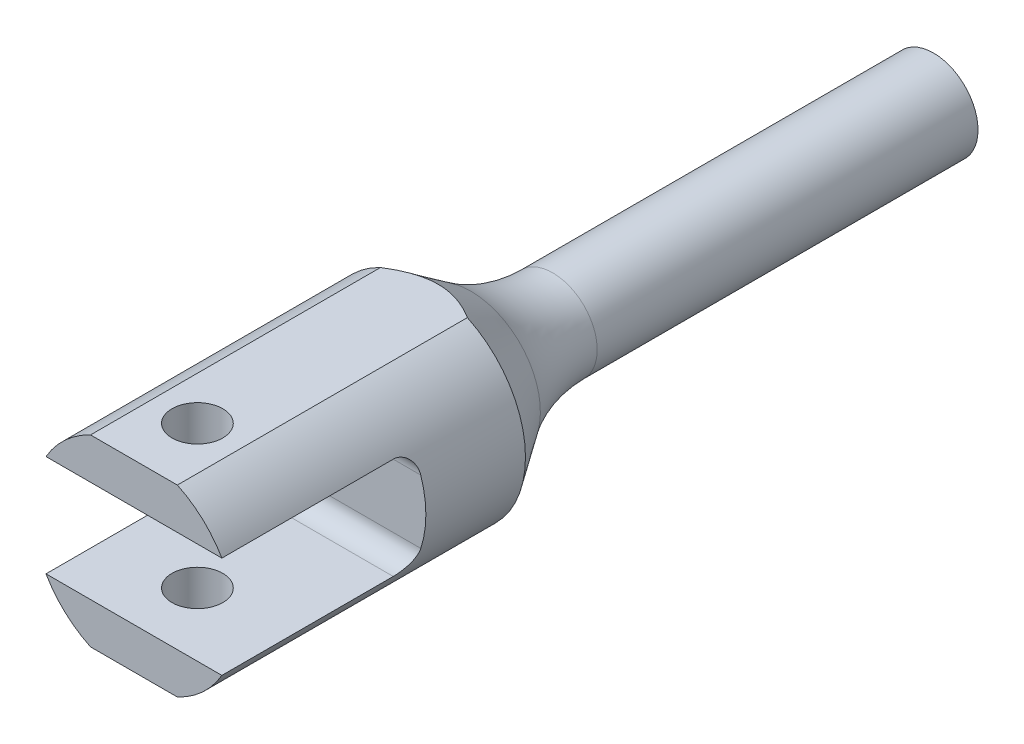
SolidWorks part; units mm, degrees
ref_plane "Front" through (0, 0, 0) normal (0, 0, 1) x (1, 0, 0)
ref_plane "Top" through (0, 0, 0) normal (0, 1, 0) x (1, 0, 0)
ref_plane "Right" through (0, 0, 0) normal (1, 0, 0) x (0, 0, -1)
sketch "Sketch1" plane through (0, 0, 0) normal (0, 0, 1) x (1, 0, 0)
  circle A0 centre (0, 0) radius 16
extrude "Boss-Extrude1" add sketch "Sketch1" along normal blind 146 contours A0
sketch "Sketch2" plane through (0, 0, 0) normal (1, 0, 0) x (0, 0, -1)
  line L0 (-146, 0) -> (-116, 0) construction
  line L1 (-146, 16) -> (-146, -16) construction
  line L2 (-116, -5) -> (-116, 5)
  line L3 (-119, 8) -> (-146, 8)
  line L4 (-119, -8) -> (-146, -8)
  line L5 (4.8369, -14.4635) -> (4.8369, -33.5991)
  line L6 (-146, 33.5991) -> (4.8369, 33.5991)
  line L7 (-146, 14.4635) -> (4.8369, 14.4635)
  line L8 (-146, 14.4635) -> (-146, 33.5991)
  line L9 (4.8369, 14.4635) -> (4.8369, 33.5991)
  line L10 (-146, -14.4635) -> (-146, -33.5991)
  line L11 (-146, -14.4635) -> (4.8369, -14.4635)
  line L12 (-146, -33.5991) -> (4.8369, -33.5991)
  line L13 (-146, 8) -> (-146, -8)
  arc A0 (-116, -5) -> (-119, -8) centre (-119, -5) cw
  arc A1 (-116, 5) -> (-119, 8) centre (-119, 5) ccw
  point P8 (-116, 0)
  point P12 (-116, -8)
  point P15 (-116, 8)
  dimension "D2" = 3
  dimension "D1" = 16
  dimension "D3" = 30
extrude "Cut-Extrude2" cut sketch "Sketch2" against normal through all both and the other way through all contours L0 L13 L4 A0 L2 | L13 L0 L2 A1 L3 | L10 L12 L5 L11 | L7 L9 L6 L8
sketch "Sketch3" plane through (0, 0, 0) normal (0, 1, 0) x (1, 0, 0)
  line L1 (0, -136) -> (0, -146) construction
  line L2 (-6.8416, -146) -> (6.8416, -146) construction
  circle A0 centre (0, -136) radius 4
  dimension "D1" = 10
  dimension "D2" = 8
extrude "Cut-Extrude3" cut sketch "Sketch3" against normal through all both and the other way through all
sketch "Sketch4" plane through (0, 0, 0) normal (1, 0, 0) x (0, 0, -1)
  line L0 (0, 0) -> (-80.5197, 0) construction
  line L1 (0, 0) -> (0, 7) construction
  line L2 (0, -14.4635) -> (0, 14.4635) construction
  line L3 (0, 7) -> (-80, 7)
  line L4 (-92.9444, 10.9883) -> (-118.2198, 28.1974)
  line L6 (-118.2198, 28.1974) -> (0, 28.1974)
  line L7 (0, 28.1974) -> (0, 7)
  arc A0 (-92.9444, 10.9883) -> (-80, 7) centre (-80, 30) ccw
  dimension "D2" = 23
  dimension "D1" = 7
  dimension "D3" = 80
revolve "Cut-Revolve3" cut sketch "Sketch4" angle 360 about L0
sketch "Sketch5" plane through (0, 0, 0) normal (1, 0, 0) x (0, 0, -1)
  line L1 (0, -12.0983) -> (-20, -12.0983)
  line L2 (0, -12.0983) -> (0, 12.0983)
  line L3 (0, 12.0983) -> (-20, 12.0983)
  line L4 (-20, -12.0983) -> (-20, 12.0983)
  dimension "D1" = 20
extrude "Cut-Extrude4" cut sketch "Sketch5" against normal through all both and the other way through all
sketch "Sketch6" plane through (0, 0, 20) normal (0, 0, -1) x (-1, 0, 0)
  circle A0 centre (0, 0) radius 4
extrude "Cut-Extrude5" cut sketch "Sketch6" against normal blind 29
